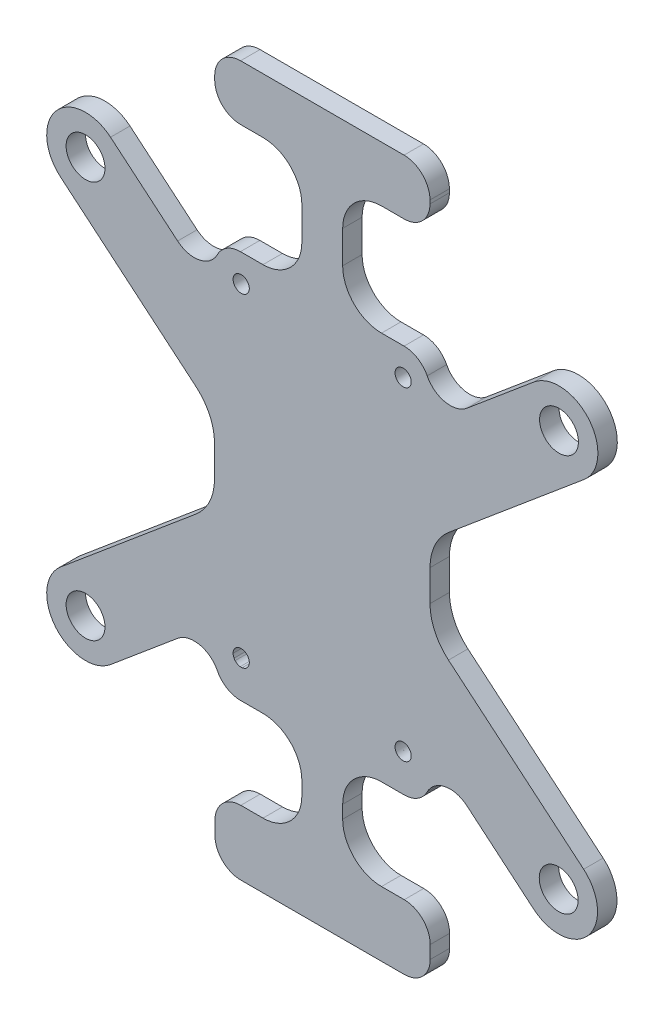
SolidWorks part; units mm, degrees
ref_plane "Front Plane" through (0, 0, 0) normal (0, 0, 1) x (1, 0, 0)
ref_plane "Top Plane" through (0, 0, 0) normal (0, 1, 0) x (1, 0, 0)
ref_plane "Right Plane" through (0, 0, 0) normal (1, 0, 0) x (0, 0, -1)
sketch "Sketch2" plane through (0, 0, 68.2352) normal (0, 0, -1) x (-1, 0, 0)
  line L0 (206.8599, 81.9145) -> (210.3184, 81.9145)
  line L2 (185.2242, 11.8921) -> (185.2242, 11.9012) construction
  line L3 (185.2242, 60.6512) -> (186.4742, 60.6512) construction
  line L4 (210.2242, 11.8921) -> (210.2242, 11.9012) construction
  line L5 (185.0827, 90.4486) -> (210.3184, 90.4486)
  line L6 (181.0827, 86.4486) -> (181.0827, 85.9145)
  line L7 (185.0827, 81.9145) -> (188.5589, 81.9145)
  line L8 (214.3184, 86.4486) -> (214.3184, 85.9145)
  line L9 (206.8599, 4.9145) -> (210.3421, 4.9145)
  line L10 (210.2829, -19.0855) -> (185.0472, -19.0855)
  line L11 (214.2829, -15.0855) -> (214.2829, -13.0855)
  line L12 (210.2829, -9.0855) -> (206.8599, -9.0855)
  line L13 (181.0472, -15.0855) -> (181.0472, -13.0855)
  line L16 (197.6946, -9.0855) -> (197.665, -9.0855)
  line L19 (194.5589, -3.0855) -> (194.5589, -1.0855)
  line L21 (200.8599, -3.0855) -> (200.8599, -1.0855)
  line L22 (181.0768, 11.9304) -> (181.0768, 13.0883)
  line L25 (194.5589, 75.9145) -> (194.5589, 70.9145)
  line L26 (186.331, 60.0703) -> (186.4379, 60.352)
  line L27 (186.4379, 60.352) -> (186.4742, 60.6512)
  line L28 (186.4742, 60.6512) -> (186.4379, 60.9503)
  line L29 (186.4379, 60.9503) -> (186.331, 61.2321)
  line L30 (186.331, 61.2321) -> (186.1599, 61.4801)
  line L31 (186.1599, 61.4801) -> (185.9343, 61.6799)
  line L32 (185.9343, 61.6799) -> (185.6675, 61.82)
  line L33 (185.6675, 61.82) -> (185.3749, 61.8921)
  line L34 (185.3749, 61.8921) -> (185.0735, 61.8921)
  line L35 (185.0735, 61.8921) -> (184.781, 61.82)
  line L36 (184.781, 61.82) -> (184.5141, 61.6799)
  line L37 (184.5141, 61.6799) -> (184.2886, 61.4801)
  line L38 (184.2886, 61.4801) -> (184.1174, 61.2321)
  line L39 (184.1174, 61.2321) -> (184.0105, 60.9503)
  line L40 (184.0105, 60.9503) -> (183.9742, 60.6512)
  line L41 (183.9742, 60.6512) -> (184.0105, 60.352)
  line L42 (184.0105, 60.352) -> (184.1174, 60.0703)
  line L43 (184.1174, 60.0703) -> (184.2886, 59.8223)
  line L44 (184.2886, 59.8223) -> (184.5141, 59.6225)
  line L45 (184.5141, 59.6225) -> (184.781, 59.4824)
  line L46 (184.781, 59.4824) -> (185.0735, 59.4103)
  line L47 (185.0735, 59.4103) -> (185.3749, 59.4103)
  line L48 (185.3749, 59.4103) -> (185.6675, 59.4824)
  line L49 (185.6675, 59.4824) -> (185.9343, 59.6225)
  line L50 (185.9343, 59.6225) -> (186.1599, 59.8223)
  line L51 (186.1599, 59.8223) -> (186.331, 60.0703)
  line L52 (186.331, 60.0703) -> (186.4379, 60.352)
  line L53 (186.4379, 60.352) -> (186.4742, 60.6512)
  line L54 (186.4742, 60.6512) -> (186.4379, 60.9503)
  line L55 (186.4379, 60.9503) -> (186.331, 61.2321)
  line L56 (186.331, 61.2321) -> (186.1599, 61.4801)
  line L57 (186.1599, 61.4801) -> (185.9343, 61.6799)
  line L58 (185.9343, 61.6799) -> (185.6675, 61.82)
  line L59 (185.6675, 61.82) -> (185.3749, 61.8921)
  line L60 (185.3749, 61.8921) -> (185.0735, 61.8921)
  line L61 (185.0735, 61.8921) -> (184.781, 61.82)
  line L62 (184.781, 61.82) -> (184.5141, 61.6799)
  line L63 (184.5141, 61.6799) -> (184.2886, 61.4801)
  line L64 (184.2886, 61.4801) -> (184.1174, 61.2321)
  line L65 (184.1174, 61.2321) -> (184.0105, 60.9503)
  line L66 (184.0105, 60.9503) -> (183.9742, 60.6512)
  line L67 (183.9742, 60.6512) -> (184.0105, 60.352)
  line L68 (184.0105, 60.352) -> (184.1174, 60.0703)
  line L69 (184.1174, 60.0703) -> (184.2886, 59.8223)
  line L70 (184.2886, 59.8223) -> (184.5141, 59.6225)
  line L71 (184.5141, 59.6225) -> (184.781, 59.4824)
  line L72 (184.781, 59.4824) -> (185.0735, 59.4103)
  line L73 (185.0735, 59.4103) -> (185.3749, 59.4103)
  line L74 (185.3749, 59.4103) -> (185.6675, 59.4824)
  line L75 (185.6675, 59.4824) -> (185.9343, 59.6225)
  line L76 (185.9343, 59.6225) -> (186.1599, 59.8223)
  line L77 (186.1599, 59.8223) -> (186.331, 60.0703)
  line L78 (210.0735, 61.8921) -> (209.781, 61.82)
  line L79 (209.781, 61.82) -> (209.5141, 61.6799)
  line L80 (209.5141, 61.6799) -> (209.2886, 61.4801)
  line L81 (209.2886, 61.4801) -> (209.1174, 61.2321)
  line L82 (209.1174, 61.2321) -> (209.0105, 60.9503)
  line L83 (209.0105, 60.9503) -> (208.9742, 60.6512)
  line L84 (208.9742, 60.6512) -> (209.0105, 60.352)
  line L85 (209.0105, 60.352) -> (209.1174, 60.0703)
  line L86 (209.1174, 60.0703) -> (209.2886, 59.8223)
  line L87 (209.2886, 59.8223) -> (209.5141, 59.6225)
  line L88 (209.5141, 59.6225) -> (209.781, 59.4824)
  line L89 (209.781, 59.4824) -> (210.0735, 59.4103)
  line L90 (210.0735, 59.4103) -> (210.3749, 59.4103)
  line L91 (210.3749, 59.4103) -> (210.6675, 59.4824)
  line L92 (210.6675, 59.4824) -> (210.9343, 59.6225)
  line L93 (210.9343, 59.6225) -> (211.1599, 59.8223)
  line L94 (211.1599, 59.8223) -> (211.331, 60.0703)
  line L95 (211.331, 60.0703) -> (211.4379, 60.352)
  line L96 (211.4379, 60.352) -> (211.4742, 60.6512)
  line L97 (211.4742, 60.6512) -> (211.4379, 60.9503)
  line L98 (211.4379, 60.9503) -> (211.331, 61.2321)
  line L99 (211.331, 61.2321) -> (211.1599, 61.4801)
  line L100 (211.1599, 61.4801) -> (210.9343, 61.6799)
  line L101 (210.9343, 61.6799) -> (210.6675, 61.82)
  line L102 (210.6675, 61.82) -> (210.3749, 61.8921)
  line L103 (210.3749, 61.8921) -> (210.0735, 61.8921)
  line L104 (210.0735, 61.8921) -> (209.781, 61.82)
  line L105 (209.781, 61.82) -> (209.5141, 61.6799)
  line L106 (209.5141, 61.6799) -> (209.2886, 61.4801)
  line L107 (209.2886, 61.4801) -> (209.1174, 61.2321)
  line L108 (209.1174, 61.2321) -> (209.0105, 60.9503)
  line L109 (209.0105, 60.9503) -> (208.9742, 60.6512)
  line L110 (208.9742, 60.6512) -> (209.0105, 60.352)
  line L111 (209.0105, 60.352) -> (209.1174, 60.0703)
  line L112 (209.1174, 60.0703) -> (209.2886, 59.8223)
  line L113 (209.2886, 59.8223) -> (209.5141, 59.6225)
  line L114 (209.5141, 59.6225) -> (209.781, 59.4824)
  line L115 (209.781, 59.4824) -> (210.0735, 59.4103)
  line L116 (210.0735, 59.4103) -> (210.3749, 59.4103)
  line L117 (210.3749, 59.4103) -> (210.6675, 59.4824)
  line L118 (210.6675, 59.4824) -> (210.9343, 59.6225)
  line L119 (210.9343, 59.6225) -> (211.1599, 59.8223)
  line L120 (211.1599, 59.8223) -> (211.331, 60.0703)
  line L121 (211.331, 60.0703) -> (211.4379, 60.352)
  line L122 (211.4379, 60.352) -> (211.4742, 60.6512)
  line L123 (211.4742, 60.6512) -> (211.4379, 60.9503)
  line L124 (211.4379, 60.9503) -> (211.331, 61.2321)
  line L125 (211.331, 61.2321) -> (211.1599, 61.4801)
  line L126 (211.1599, 61.4801) -> (210.9343, 61.6799)
  line L127 (210.9343, 61.6799) -> (210.6675, 61.82)
  line L128 (210.6675, 61.82) -> (210.3749, 61.8921)
  line L129 (210.3749, 61.8921) -> (210.0735, 61.8921)
  line L130 (186.1599, 11.4801) -> (185.9343, 11.6799)
  line L131 (185.9343, 11.6799) -> (185.6675, 11.82)
  line L132 (185.6675, 11.82) -> (185.3749, 11.8921)
  line L133 (185.3749, 11.8921) -> (185.0735, 11.8921)
  line L134 (185.0735, 11.8921) -> (184.781, 11.82)
  line L135 (184.781, 11.82) -> (184.5141, 11.6799)
  line L136 (184.5141, 11.6799) -> (184.2886, 11.4801)
  line L137 (184.2886, 11.4801) -> (184.1174, 11.2321)
  line L138 (184.1174, 11.2321) -> (184.0105, 10.9503)
  line L139 (184.0105, 10.9503) -> (183.9742, 10.6512)
  line L140 (183.9742, 10.6512) -> (184.0105, 10.352)
  line L141 (184.0105, 10.352) -> (184.1174, 10.0703)
  line L142 (184.1174, 10.0703) -> (184.2886, 9.8223)
  line L143 (184.2886, 9.8223) -> (184.5141, 9.6225)
  line L144 (184.5141, 9.6225) -> (184.781, 9.4824)
  line L145 (184.781, 9.4824) -> (185.0735, 9.4103)
  line L146 (185.0735, 9.4103) -> (185.3749, 9.4103)
  line L147 (185.3749, 9.4103) -> (185.6675, 9.4824)
  line L148 (185.6675, 9.4824) -> (185.9343, 9.6225)
  line L149 (185.9343, 9.6225) -> (186.1599, 9.8223)
  line L150 (186.1599, 9.8223) -> (186.331, 10.0703)
  line L151 (186.331, 10.0703) -> (186.4379, 10.352)
  line L152 (186.4379, 10.352) -> (186.4742, 10.6512)
  line L153 (186.4742, 10.6512) -> (186.4379, 10.9503)
  line L154 (186.4379, 10.9503) -> (186.331, 11.2321)
  line L155 (186.331, 11.2321) -> (186.1599, 11.4801)
  line L156 (186.1599, 11.4801) -> (185.9343, 11.6799)
  line L157 (185.9343, 11.6799) -> (185.6675, 11.82)
  line L158 (185.6675, 11.82) -> (185.3749, 11.8921)
  line L159 (185.3749, 11.8921) -> (185.0735, 11.8921)
  line L160 (185.0735, 11.8921) -> (184.781, 11.82)
  line L161 (184.781, 11.82) -> (184.5141, 11.6799)
  line L162 (184.5141, 11.6799) -> (184.2886, 11.4801)
  line L163 (184.2886, 11.4801) -> (184.1174, 11.2321)
  line L164 (184.1174, 11.2321) -> (184.0105, 10.9503)
  line L165 (184.0105, 10.9503) -> (183.9742, 10.6512)
  line L166 (183.9742, 10.6512) -> (184.0105, 10.352)
  line L167 (184.0105, 10.352) -> (184.1174, 10.0703)
  line L168 (184.1174, 10.0703) -> (184.2886, 9.8223)
  line L169 (184.2886, 9.8223) -> (184.5141, 9.6225)
  line L170 (184.5141, 9.6225) -> (184.781, 9.4824)
  line L171 (184.781, 9.4824) -> (185.0735, 9.4103)
  line L172 (185.0735, 9.4103) -> (185.3749, 9.4103)
  line L173 (185.3749, 9.4103) -> (185.6675, 9.4824)
  line L174 (185.6675, 9.4824) -> (185.9343, 9.6225)
  line L175 (185.9343, 9.6225) -> (186.1599, 9.8223)
  line L176 (186.1599, 9.8223) -> (186.331, 10.0703)
  line L177 (186.331, 10.0703) -> (186.4379, 10.352)
  line L178 (186.4379, 10.352) -> (186.4742, 10.6512)
  line L179 (186.4742, 10.6512) -> (186.4379, 10.9503)
  line L180 (186.4379, 10.9503) -> (186.331, 11.2321)
  line L181 (186.331, 11.2321) -> (186.1599, 11.4801)
  line L182 (208.9742, 10.6512) -> (209.0105, 10.352)
  line L183 (209.0105, 10.352) -> (209.1174, 10.0703)
  line L184 (209.1174, 10.0703) -> (209.2886, 9.8223)
  line L185 (209.2886, 9.8223) -> (209.5141, 9.6225)
  line L186 (209.5141, 9.6225) -> (209.781, 9.4824)
  line L187 (209.781, 9.4824) -> (210.0735, 9.4103)
  line L188 (210.0735, 9.4103) -> (210.3749, 9.4103)
  line L189 (210.3749, 9.4103) -> (210.6675, 9.4824)
  line L190 (210.6675, 9.4824) -> (210.9343, 9.6225)
  line L191 (210.9343, 9.6225) -> (211.1599, 9.8223)
  line L192 (211.1599, 9.8223) -> (211.331, 10.0703)
  line L193 (211.331, 10.0703) -> (211.4379, 10.352)
  line L194 (211.4379, 10.352) -> (211.4742, 10.6512)
  line L195 (211.4742, 10.6512) -> (211.4379, 10.9503)
  line L196 (211.4379, 10.9503) -> (211.331, 11.2321)
  line L197 (211.331, 11.2321) -> (211.1599, 11.4801)
  line L198 (211.1599, 11.4801) -> (210.9343, 11.6799)
  line L199 (210.9343, 11.6799) -> (210.6675, 11.82)
  line L200 (210.6675, 11.82) -> (210.3749, 11.8921)
  line L201 (210.3749, 11.8921) -> (210.0735, 11.8921)
  line L202 (210.0735, 11.8921) -> (209.781, 11.82)
  line L203 (209.781, 11.82) -> (209.5141, 11.6799)
  line L204 (209.5141, 11.6799) -> (209.2886, 11.4801)
  line L205 (209.2886, 11.4801) -> (209.1174, 11.2321)
  line L206 (209.1174, 11.2321) -> (209.0105, 10.9503)
  line L207 (209.0105, 10.9503) -> (208.9742, 10.6512)
  line L208 (208.9742, 10.6512) -> (209.0105, 10.352)
  line L209 (209.0105, 10.352) -> (209.1174, 10.0703)
  line L210 (209.1174, 10.0703) -> (209.2886, 9.8223)
  line L211 (209.2886, 9.8223) -> (209.5141, 9.6225)
  line L212 (209.5141, 9.6225) -> (209.781, 9.4824)
  line L213 (209.781, 9.4824) -> (210.0735, 9.4103)
  line L214 (210.0735, 9.4103) -> (210.3749, 9.4103)
  line L215 (210.3749, 9.4103) -> (210.6675, 9.4824)
  line L216 (210.6675, 9.4824) -> (210.9343, 9.6225)
  line L217 (210.9343, 9.6225) -> (211.1599, 9.8223)
  line L218 (211.1599, 9.8223) -> (211.331, 10.0703)
  line L219 (211.331, 10.0703) -> (211.4379, 10.352)
  line L220 (211.4379, 10.352) -> (211.4742, 10.6512)
  line L221 (211.4742, 10.6512) -> (211.4379, 10.9503)
  line L222 (211.4379, 10.9503) -> (211.331, 11.2321)
  line L223 (211.331, 11.2321) -> (211.1599, 11.4801)
  line L224 (211.1599, 11.4801) -> (210.9343, 11.6799)
  line L225 (210.9343, 11.6799) -> (210.6675, 11.82)
  line L226 (210.6675, 11.82) -> (210.3749, 11.8921)
  line L227 (210.3749, 11.8921) -> (210.0735, 11.8921)
  line L228 (210.0735, 11.8921) -> (209.781, 11.82)
  line L229 (209.781, 11.82) -> (209.5141, 11.6799)
  line L230 (209.5141, 11.6799) -> (209.2886, 11.4801)
  line L231 (209.2886, 11.4801) -> (209.1174, 11.2321)
  line L232 (209.1174, 11.2321) -> (209.0105, 10.9503)
  line L233 (209.0105, 10.9503) -> (208.9742, 10.6512)
  line L235 (200.8599, 75.9145) -> (200.8599, 70.9145)
  line L238 (185.0768, 64.9145) -> (188.5589, 64.9145)
  line L239 (181.0768, 60.9145) -> (181.0768, 56.6869)
  line L240 (185.0768, 4.9145) -> (188.5589, 4.9145)
  line L241 (214.3421, 60.9145) -> (214.3421, 56.701)
  line L243 (208.9742, 60.6512) -> (210.2242, 60.6512) construction
  line L244 (185.2242, 59.4012) -> (185.2242, 60.6512) construction
  line L245 (210.2242, 59.4012) -> (210.2242, 59.4103) construction
  line L246 (188.5589, -9.0855) -> (185.0472, -9.0855)
  line L249 (197.6946, -9.0855) -> (197.665, -9.0855)
  line L250 (206.8599, 64.9145) -> (210.3421, 64.9145)
  line L252 (214.3421, 11.9304) -> (214.3421, 13.1358)
  line L253 (181.0768, 48.8739) -> (181.0768, 48.857)
  line L257 (181.0768, 11.9304) -> (181.0768, 8.9145)
  line L258 (214.3421, 11.9304) -> (214.3421, 8.9145)
  line L259 (214.3421, 32.528) -> (214.3421, 37.3015)
  line L268 (161.2114, 4.2381) -> (163.5085, 6.1676) construction
  line L269 (157.3523, 8.8324) -> (178.2221, 26.362)
  line L270 (165.0704, -0.3563) -> (181.0768, 13.0883)
  line L271 (161.1574, 65.5584) -> (163.4562, 63.6309) construction
  line L272 (165.0123, 70.1562) -> (181.0768, 56.6869)
  line L273 (157.3024, 60.9607) -> (178.2167, 43.425)
  line L274 (163.4572, 63.6321) -> (161.1574, 65.5584) construction
  line L276 (181.0768, 37.2947) -> (181.0768, 32.4878)
  line L279 (181.0768, 34.9304) -> (157.715, 34.9304) construction
  line L281 (214.3421, 56.701) -> (230.3954, 70.1849)
  line L284 (214.3421, 13.1358) -> (230.3994, -0.3275)
  line L287 (163.5078, 6.1685) -> (161.2114, 4.2381) construction
  line L288 (231.9555, 6.1977) -> (234.2544, 4.2703) construction
  line L289 (231.9562, 6.1986) -> (234.2544, 4.2703) construction
  line L290 (231.9572, 63.6611) -> (234.2544, 65.5906) construction
  line L291 (231.9562, 63.6622) -> (234.2544, 65.5906) construction
  line L294 (217.1967, 43.4273) -> (238.1134, 60.9963)
  line L295 (214.3421, 34.9304) -> (237.715, 34.9304) construction
  line L296 (217.2021, 26.3977) -> (238.1093, 8.868)
  line L297 (214.3421, 48.8652) -> (214.3421, 48.8822)
  circle A0 centre (210.2242, 60.6512) radius 1.25
  circle A1 centre (185.2242, 60.6512) radius 1.25
  circle A2 centre (210.2242, 10.6512) radius 1.25
  circle A3 centre (185.2242, 10.6512) radius 1.25
  arc A4 (210.3421, 64.9145) -> (214.3421, 60.9145) centre (210.3421, 60.9145) cw
  arc A5 (185.0768, 64.9145) -> (181.0768, 60.9145) centre (185.0768, 60.9145) ccw
  arc A6 (181.0827, 85.9145) -> (185.0827, 81.9145) centre (185.0827, 85.9145) ccw
  arc A7 (185.0827, 90.4486) -> (181.0827, 86.4486) centre (185.0827, 86.4486) ccw
  arc A8 (210.3184, 90.4486) -> (214.3184, 86.4486) centre (210.3184, 86.4486) cw
  arc A9 (210.3184, 81.9145) -> (214.3184, 85.9145) centre (210.3184, 85.9145) ccw
  arc A10 (181.0768, 8.9145) -> (185.0768, 4.9145) centre (185.0768, 8.9145) ccw
  arc A11 (210.3421, 4.9145) -> (214.3421, 8.9145) centre (210.3421, 8.9145) ccw
  arc A12 (214.2829, -13.0855) -> (210.2829, -9.0855) centre (210.2829, -13.0855) ccw
  arc A13 (185.0472, -9.0855) -> (181.0472, -13.0855) centre (185.0472, -13.0855) ccw
  arc A14 (210.2829, -19.0855) -> (214.2829, -15.0855) centre (210.2829, -15.0855) ccw
  arc A15 (185.0472, -19.0855) -> (181.0472, -15.0855) centre (185.0472, -15.0855) cw
  arc A16 (194.5589, -3.0855) -> (188.5589, -9.0855) centre (188.5589, -3.0855) cw
  arc A17 (194.5589, -1.0855) -> (188.5589, 4.9145) centre (188.5589, -1.0855) ccw
  arc A18 (200.8599, -1.0855) -> (206.8599, 4.9145) centre (206.8599, -1.0855) cw
  arc A19 (206.8599, -9.0855) -> (200.8599, -3.0855) centre (206.8599, -3.0855) cw
  arc A20 (194.5589, 75.9145) -> (188.5589, 81.9145) centre (188.5589, 75.9145) ccw
  arc A21 (194.5589, 70.9145) -> (188.5589, 64.9145) centre (188.5589, 70.9145) cw
  arc A22 (200.8599, 70.9145) -> (206.8599, 64.9145) centre (206.8599, 70.9145) ccw
  arc A23 (200.8599, 75.9145) -> (206.8599, 81.9145) centre (206.8599, 75.9145) cw
  arc A24 (157.3523, 8.8324) -> (165.0704, -0.3563) centre (161.2114, 4.2381) ccw
  arc A25 (238.1134, 60.9963) -> (230.3954, 70.1849) centre (234.2544, 65.5906) ccw
  arc A26 (165.0123, 70.1562) -> (157.3024, 60.9607) centre (161.1574, 65.5584) ccw
  arc A27 (230.3994, -0.3275) -> (238.1093, 8.868) centre (234.2544, 4.2703) ccw
  circle A28 centre (161.1574, 65.5584) radius 3
  circle A29 centre (161.2114, 4.2381) radius 3
  circle A30 centre (234.2544, 65.5906) radius 3
  circle A31 centre (234.2544, 4.2703) radius 3
  arc A32 (214.3421, 32.528) -> (217.2021, 26.3977) centre (222.3421, 32.528) ccw
  arc A33 (217.1967, 43.4273) -> (214.3421, 37.3015) centre (222.3421, 37.3015) ccw
  arc A34 (178.2221, 26.362) -> (181.0768, 32.4878) centre (173.0768, 32.4878) ccw
  arc A35 (181.0768, 37.2947) -> (178.2167, 43.425) centre (173.0768, 37.2947) ccw
  point P124 (197.7242, 0.7556)
  point P131 (197.7094, 71.2884)
  point P178 (200.8599, 4.9145)
  point P187 (200.8599, 64.9145)
  point P190 (200.8599, 81.9145)
  point P191 (197.715, 34.9304)
  point P195 (197.715, 34.9304)
  point P207 (197.7329, 34.9143)
  point P215 (197.7059, 34.9143)
  dimension "D5" = 17
  dimension "D9" = 4
  dimension "D10" = 6
  dimension "D11" = 8
  dimension "D6" = 14
  dimension "D7" = 6.301
  dimension "D8" = 6.301
  dimension "D1" = 0
  dimension "D2" = 0
  dimension "D3" = 0
  dimension "D4" = 0
extrude "Boss-Extrude1" add sketch "Sketch2" along normal blind 3
fillet "Fillet1" radius 4 4 edges at (-181.0768, 13.0883, 66.7352) (-214.3421, 13.1358, 66.7352) (-214.3421, 56.701, 66.7352) (-181.0768, 56.6869, 66.7352)
